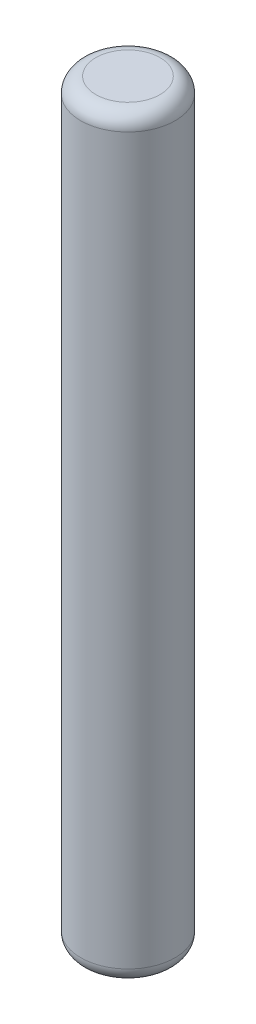
SolidWorks part; units mm, degrees
ref_plane "Front" through (0, 0, 0) normal (0, 0, 1) x (1, 0, 0)
ref_plane "Top" through (0, 0, 0) normal (0, 1, 0) x (1, 0, 0)
ref_plane "Right" through (0, 0, 0) normal (1, 0, 0) x (0, 0, -1)
sketch "Sketch1" plane through (0, 0, 0) normal (0, 1, 0) x (1, 0, 0)
  circle A0 centre (0, 0) radius 1.5875
  dimension "D1" = 3.175
extrude "Extrude1" add sketch "Sketch1" along normal blind 25.4
fillet "Fillet1" radius 0.508 2 edges at (0, 0, 1.5875) (0, 25.4, 1.5875)
